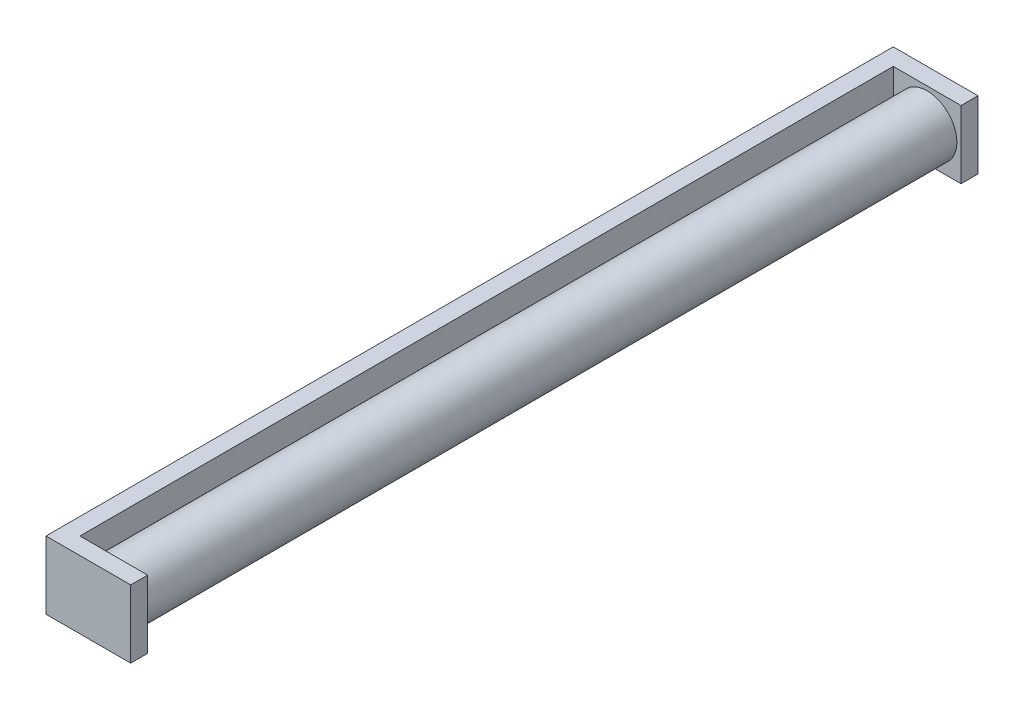
SolidWorks part; units mm, degrees
material "玻璃"
ref_plane "前视基准面" through (0, 0, 0) normal (0, 0, 1) x (1, 0, 0)
ref_plane "上视基准面" through (0, 0, 0) normal (0, 1, 0) x (1, 0, 0)
ref_plane "右视基准面" through (0, 0, 0) normal (1, 0, 0) x (0, 0, -1)
sketch "草图1" plane through (0, 0, 0) normal (1, 0, 0) x (0, 0, -1)
  line L1 (-500, -40) -> (500, -40)
  line L2 (-500, -40) -> (-500, 40)
  line L3 (-500, 40) -> (500, 40)
  line L4 (500, -40) -> (500, 40)
  line L5 (-500, -40) -> (500, 40) construction
  line L6 (-500, 40) -> (500, -40) construction
  point P0 (0, 0)
  dimension "D1" = 1000
  dimension "D2" = 80
extrude "凸台-拉伸1" add sketch "草图1" along normal blind 20
sketch "草图2" plane through (20, 0, 0) normal (1, 0, 0) x (0, 0, -1)
  line L0 (-500, 40) -> (-500, -40) construction
  line L1 (-500, 40) -> (-500, -40)
extrude "拉伸-薄壁1" add sketch "草图2" along normal blind 80 thin thin type one direction reverse wall 20
mirror "镜向1" about plane through (0, 0, 0) normal (0, 0, 1) of "拉伸-薄壁1"
sketch "草图3" plane through (0, 0, 500) normal (0, 0, 1) x (1, 0, 0)
  line L0 (100, 40) -> (100, -40) construction
  line L1 (100, 40) -> (20, 40) construction
  circle A0 centre (60, 0) radius 35
  point P2 (100, 0)
  point P7 (60, 40)
  dimension "D1" = 70
extrude "凸台-拉伸2" add sketch "草图3" against normal up to surface (980 mm away) up to face at (60, 0, -480)
